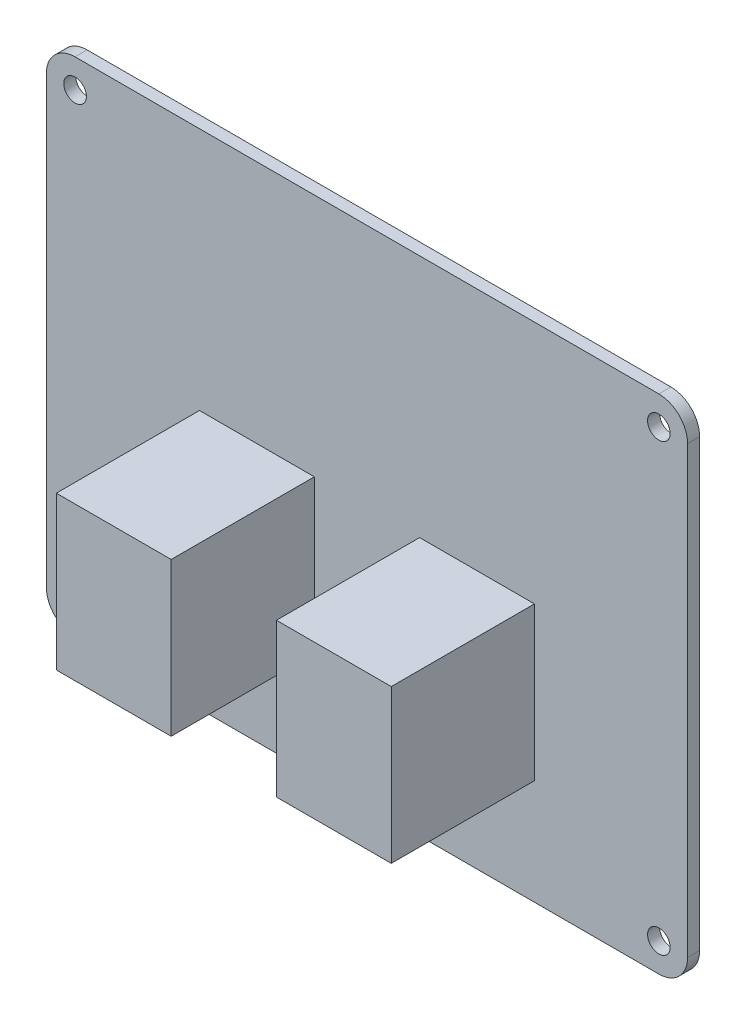
SolidWorks part; units mm, degrees
ref_plane "前视基准面" through (0, 0, 0) normal (0, 0, 1) x (1, 0, 0)
ref_plane "上视基准面" through (0, 0, 0) normal (0, 1, 0) x (1, 0, 0)
ref_plane "右视基准面" through (0, 0, 0) normal (1, 0, 0) x (0, 0, -1)
ref_plane "基准面4" through (0, 0, 1.6) normal (0, 0, 1) x (1, 0, 0)
sketch "草图1" plane through (0, 0, 1.6) normal (0, 0, 1) x (1, 0, 0)
  line L0 (85.09, 0) -> (85.09, 66.675)
  line L1 (85.09, 66.675) -> (0, 66.675)
  line L2 (0, 66.675) -> (0, 0)
  line L3 (0, 0) -> (85.09, 0)
extrude "凸台-拉伸1" add sketch "草图1" against normal blind 1.6
sketch "草图2" plane through (0, 0, 1.6) normal (0, 0, 1) x (1, 0, 0)
  line L0 (49.53, 34.29) -> (64.77, 34.29)
  line L1 (64.77, 34.29) -> (64.77, 13.97)
  line L2 (64.77, 13.97) -> (49.53, 13.97)
  line L3 (49.53, 13.97) -> (49.53, 34.29)
extrude "凸台-拉伸2" add sketch "草图2" along normal blind 19
sketch "草图3" plane through (0, 0, 1.6) normal (0, 0, 1) x (1, 0, 0)
  line L0 (35.56, 13.97) -> (20.32, 13.97)
  line L1 (20.32, 13.97) -> (20.32, 34.29)
  line L2 (20.32, 34.29) -> (35.56, 34.29)
  line L3 (35.56, 34.29) -> (35.56, 13.97)
extrude "凸台-拉伸3" add sketch "草图3" along normal blind 19
hole_wizard "Ø3.0 (3) 直径孔1" positions "草图5" profile "草图4" hole size "Ø3.0" standard "ANSI Metric"
sketch "草图5" plane through (0, 0, 0) normal (0, 0, -1) x (-1, 0, 0)
  point P0 (-3.81, 62.865)
  point P1 (-3.81, 3.81)
  point P2 (-81.28, 3.81)
  point P3 (-81.28, 62.865)
sketch "草图4" plane through (3.81, 62.865, 0) normal (1, 0, 0) x (0, 1, 0)
  line L0 (0, 0) -> (0, 20.6)
  line L1 (0, 20.6) -> (1.5, 20.6)
  line L2 (1.5, 20.6) -> (1.5, 0)
  line L5 (1.5, 0) -> (0, 0)
  line L11 (0, -6.35) -> (0, 107.95) construction
  dimension "通孔孔直径" = 3
  dimension "通孔孔深度" = 20.6
fillet "圆角1" radius 3.81 4 edges at (85.09, 0, 0.8) (0, 0, 0.8) (85.09, 66.675, 0.8) (0, 66.675, 0.8)
